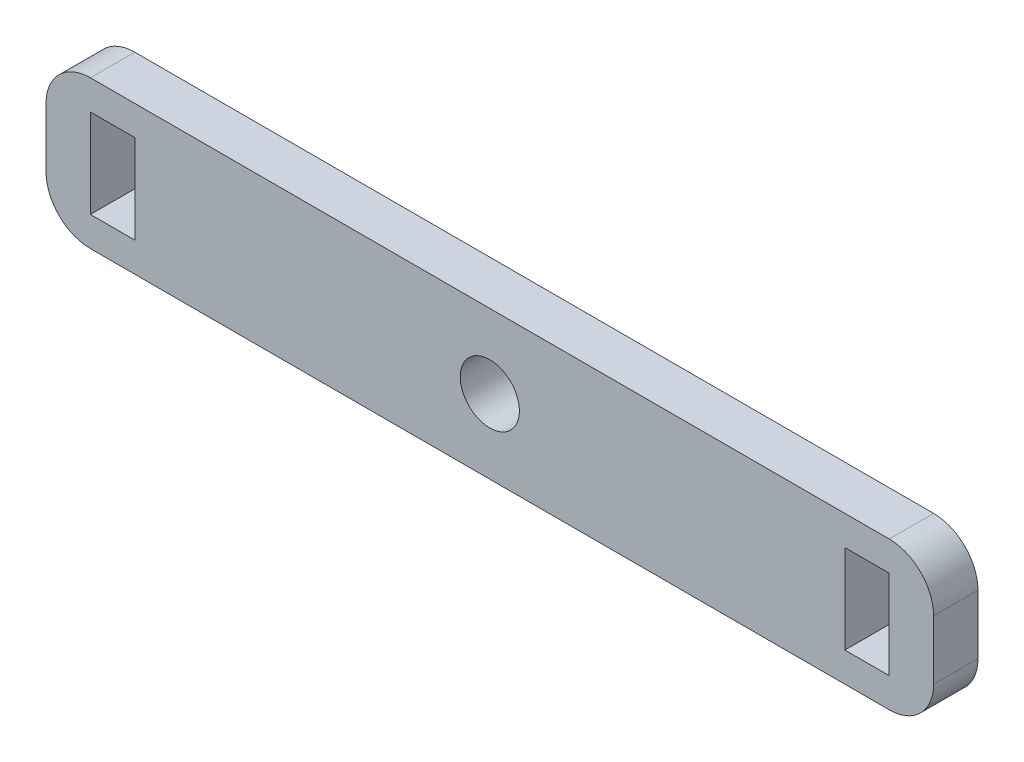
SolidWorks part; units mm, degrees
ref_plane "Front Plane" through (0, 0, 0) normal (0, 0, 1) x (1, 0, 0)
ref_plane "Top Plane" through (0, 0, 0) normal (0, 1, 0) x (1, 0, 0)
ref_plane "Right Plane" through (0, 0, 0) normal (1, 0, 0) x (0, 0, -1)
sketch "Sketch1" plane through (0, 0, 0) normal (0, 0, 1) x (1, 0, 0)
  line L1 (-30, 5) -> (30, 5)
  line L2 (-30, 5) -> (-30, -5)
  line L3 (-30, -5) -> (30, -5)
  line L4 (30, 5) -> (30, -5)
  line L5 (-30, 5) -> (30, -5) construction
  line L6 (-30, -5) -> (30, 5) construction
  point P0 (0, 0)
  dimension "D1" = 60
  dimension "D2" = 10
extrude "Boss-Extrude1" add sketch "Sketch1" along normal blind 3
sketch "Sketch2" plane through (0, 0, 3) normal (0, 0, 1) x (1, 0, 0)
  circle A0 centre (0, 0) radius 2
extrude "Cut-Extrude1" cut sketch "Sketch2" against normal blind 3
sketch "Sketch3" plane through (0, 0, 3) normal (0, 0, 1) x (1, 0, 0)
  line L0 (-30, 5) -> (-30, -5) construction
  line L1 (-27, 3) -> (-24, 3)
  line L2 (-27, 3) -> (-27, -3)
  line L3 (-27, -3) -> (-24, -3)
  line L4 (-24, 3) -> (-24, -3)
  line L5 (-30, -5) -> (30, -5) construction
  line L6 (30, 5) -> (-30, 5) construction
  dimension "D1" = 3
  dimension "D2" = 2
  dimension "D3" = 2
  dimension "D4" = 3
extrude "Cut-Extrude2" cut sketch "Sketch3" against normal blind 3
mirror "Mirror1" about plane through (0, 0, 0) normal (1, 0, 0) of "Cut-Extrude2"
fillet "Fillet1" radius 3 4 edges at (-30, -5, 1.5) (-30, 5, 1.5) (30, -5, 1.5) (30, 5, 1.5)
